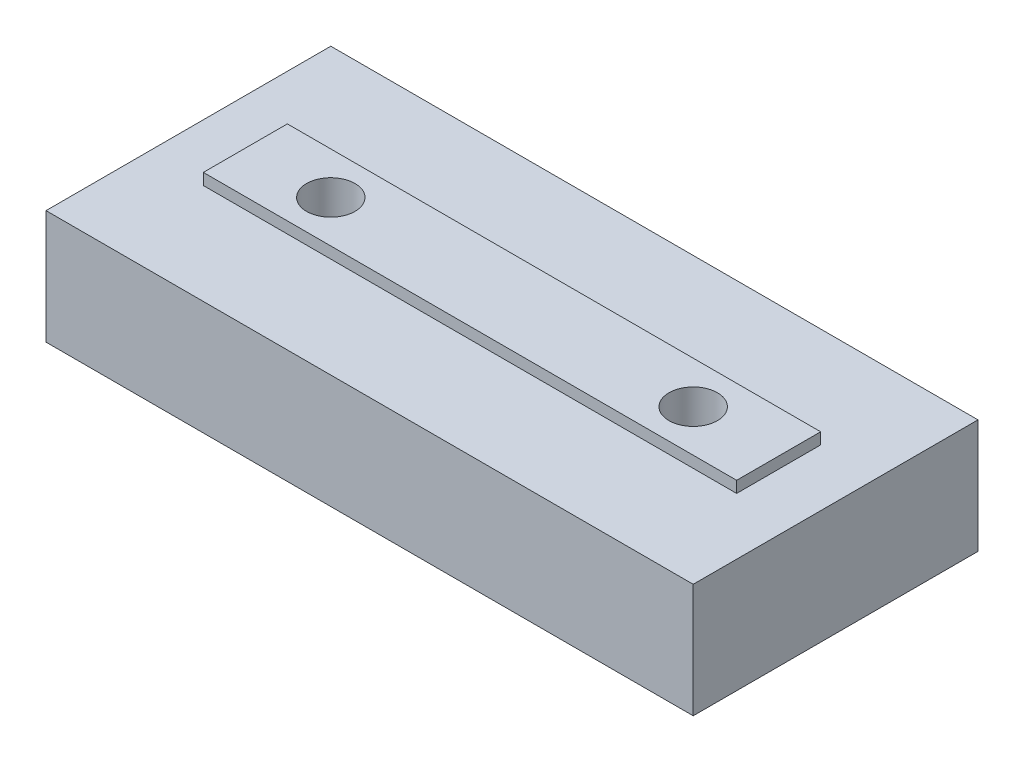
SolidWorks part; units mm, degrees
other "Markup1"
sketch "Sketch5" plane through (-15.0702, 0, -8.0763) normal (-0.3862, -0.9, -0.202) x (-0.7575, 0.1845, 0.6263)
ref_plane "Front Plane" through (0, 0, 0) normal (0, 0, 1) x (1, 0, 0)
ref_plane "Top Plane" through (0, 0, 0) normal (0, 1, 0) x (1, 0, 0)
ref_plane "Right Plane" through (0, 0, 0) normal (1, 0, 0) x (0, 0, -1)
sketch "Sketch1" plane through (0, 0, 0) normal (0, 1, 0) x (1, 0, 0)
  line L1 (-15.0702, 8.0763) -> (30.3798, 8.0763)
  line L2 (-15.0702, 8.0763) -> (-15.0702, -11.9237)
  line L3 (-15.0702, -11.9237) -> (30.3798, -11.9237)
  line L4 (30.3798, 8.0763) -> (30.3798, -11.9237)
extrude "Boss-Extrude1" add sketch "Sketch1" along normal blind 8 contours L1 L4 L3 L2
sketch "Sketch2" plane through (0, 8, 0) normal (0, 1, 0) x (1, 0, 0)
  line L0 (-15.0702, -1.9237) -> (30.3798, -1.9237) construction
  line L2 (-15.0702, 8.0763) -> (-15.0702, -11.9237) construction
  line L4 (-11.0702, 1.0263) -> (-11.0702, -4.8737)
  line L5 (-11.0702, 1.0263) -> (26.3798, 1.0263)
  line L7 (-11.0702, -4.8737) -> (26.3798, -4.8737)
  line L8 (26.3798, 1.0263) -> (26.3798, -4.8737)
  line L9 (30.3798, 8.0763) -> (30.3798, -11.9237) construction
  point P13 (26.3798, -1.9237)
  point P14 (-11.0702, -1.9237)
  dimension "D1" = 5.9
  dimension "D2" = 4
  dimension "D3" = 4
extrude "Boss-Extrude2" add sketch "Sketch2" along normal blind 0.8 contours L7 L8 L5 L4
ref_plane "Plane1" through (7.6548, 0, 0) normal (-1, 0, 0) x (0, 0, 1)
hole_wizard "M3 Clearance Hole1" positions "Sketch3" profile "Sketch4" hole size "M3" standard "DIN" end condition through all
sketch "Sketch3" plane through (0, 0, 0) normal (0, -1, 0) x (-1, 0, 0)
  line L1 (-7.6548, -9.9397) -> (-7.6548, 9.9397) construction
  line L4 (-30.3798, -1.9237) -> (15.0702, -1.9237) construction
  line L5 (-30.3798, 8.0763) -> (-30.3798, -11.9237) construction
  line L6 (15.0702, 8.0763) -> (15.0702, -11.9237) construction
  point P0 (-20.3798, -1.9237)
  point P12 (5.0702, -1.9237)
  dimension "D1" = 10
sketch "Sketch4" plane through (20.3798, 0, 1.9237) normal (1, 0, 0) x (0, 0, -1)
  line L0 (0, 0) -> (0, 8.8)
  line L1 (0, 8.8) -> (1.7, 8.8)
  line L2 (1.7, 8.8) -> (1.7, 0)
  line L5 (1.7, 0) -> (0, 0)
  line L11 (0, -6.35) -> (0, 107.95) construction
  dimension "Thru Hole Dia." = 3.4
  dimension "Thru Hole Depth" = 8.8
